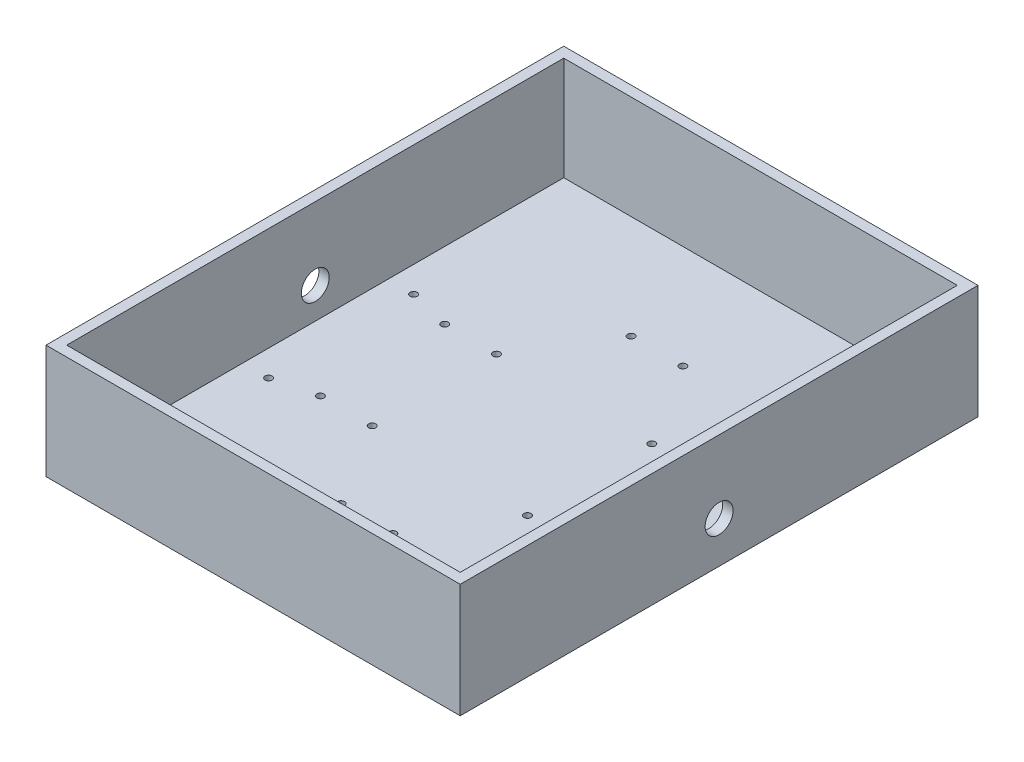
SolidWorks part; units mm, degrees
ref_plane "Front Plane" through (0, 0, 0) normal (0, 0, 1) x (1, 0, 0)
ref_plane "Top Plane" through (0, 0, 0) normal (0, 1, 0) x (1, 0, 0)
ref_plane "Right Plane" through (0, 0, 0) normal (1, 0, 0) x (0, 0, -1)
sketch "Sketch1" plane through (0, 0, 0) normal (0, 0, 1) x (1, 0, 0)
  line L0 (0, 50) -> (0, 0) construction
  line L1 (-95, 0) -> (95, 0)
  line L2 (-95, 0) -> (-95, 50)
  line L3 (-95, 50) -> (95, 50)
  line L4 (95, 0) -> (95, 50)
  dimension "D1" = 190
  dimension "D2" = 50
extrude "Boss-Extrude1" add sketch "Sketch1" along normal mid plane 240
shell "Shell1" thickness 5
sketch "Sketch2" plane through (0, 0, 0) normal (0, 1, 0) x (1, 0, 0)
  line L0 (-26.87, 0) -> (34.5029, 0) construction
  line L1 (0, -20.877) -> (0, 39.4378) construction
  circle A12 centre (-12.5, 70) radius 1.7
  circle A13 centre (-37.5, 30) radius 1.7
  circle A14 centre (-62.5, 30) radius 1.7
  circle A15 centre (-82.5, 35) radius 1.7
  circle A28 centre (82.5, 35) radius 1.7
  circle A29 centre (62.5, 30) radius 1.7
  circle A30 centre (37.5, 30) radius 1.7
  circle A31 centre (12.5, 70) radius 1.7
  circle A32 centre (12.5, -70) radius 1.7
  circle A33 centre (37.5, -30) radius 1.7
  circle A34 centre (62.5, -30) radius 1.7
  circle A35 centre (82.5, -35) radius 1.7
  circle A36 centre (-82.5, -35) radius 1.7
  circle A37 centre (-62.5, -30) radius 1.7
  circle A38 centre (-37.5, -30) radius 1.7
  circle A39 centre (-12.5, -70) radius 1.7
  point P3 (0, 0)
  dimension "D8" = 3.4
  dimension "D1" = 25
  dimension "D2" = 20
  dimension "D3" = 5
  dimension "D4" = 40
  dimension "D5" = 30
  dimension "D6" = 25
  dimension "D7" = 12.5
extrude "Cut-Extrude1" cut sketch "Sketch2" against normal through all both and the other way through all
sketch "Sketch3" plane through (0, 0, 0) normal (1, 0, 0) x (0, 0, -1)
  line L0 (-125, -5) -> (125, -5) construction
  circle A0 centre (0, 15) radius 6.75
  dimension "D2" = 13.5
  dimension "D1" = 20
extrude "Cut-Extrude2" cut sketch "Sketch3" against normal through all both and the other way through all
